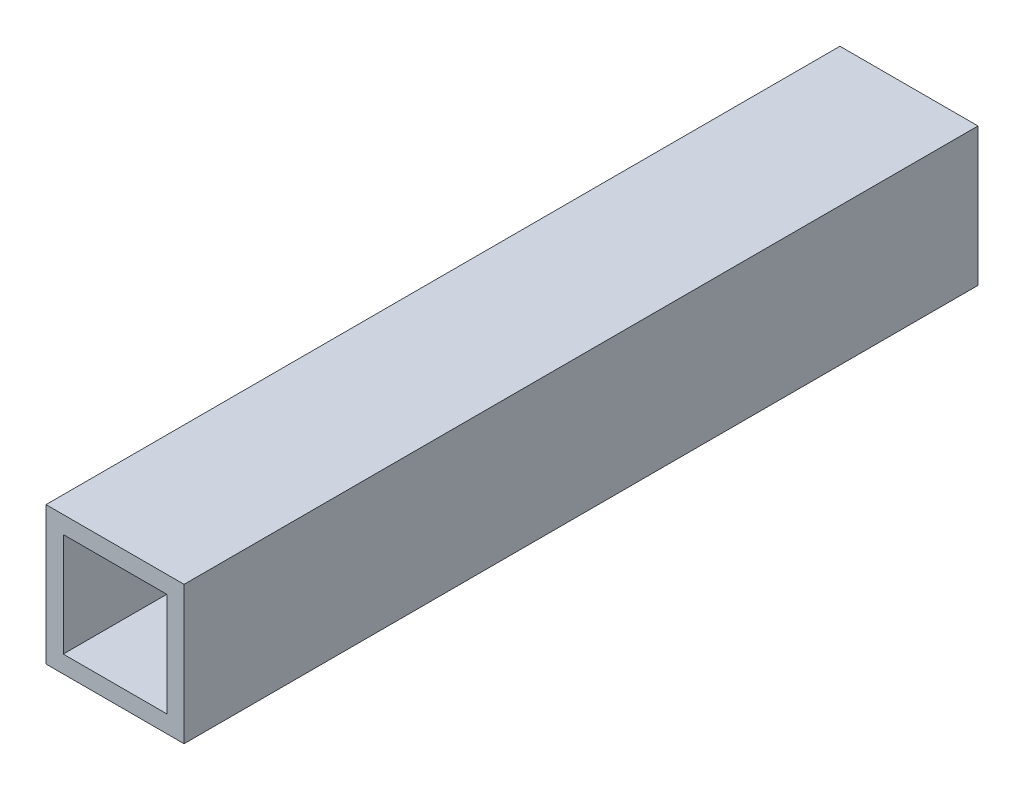
SolidWorks part; units mm, degrees
ref_plane "Front Plane" through (0, 0, 0) normal (0, 0, 1) x (1, 0, 0)
ref_plane "Top Plane" through (0, 0, 0) normal (0, 1, 0) x (1, 0, 0)
ref_plane "Right Plane" through (0, 0, 0) normal (1, 0, 0) x (0, 0, -1)
sketch "Sketch1" plane through (0, 0, 0) normal (0, 0, 1) x (1, 0, 0)
  line L0 (-20, 20) -> (20, 20)
  line L1 (-15, 15) -> (15, 15)
  line L2 (-15, 15) -> (-15, -15)
  line L3 (-15, -15) -> (15, -15)
  line L4 (15, 15) -> (15, -15)
  line L5 (-15, 15) -> (15, -15) construction
  line L6 (-15, -15) -> (15, 15) construction
  line L7 (20, 20) -> (20, -20)
  line L8 (-20, -20) -> (20, -20)
  line L9 (-20, 20) -> (-20, -20)
  point P0 (0, 0)
  dimension "D1" = 30
  dimension "D2" = 30
  dimension "D3" = 5
extrude "Boss-Extrude5" add sketch "Sketch1" along normal blind 230
